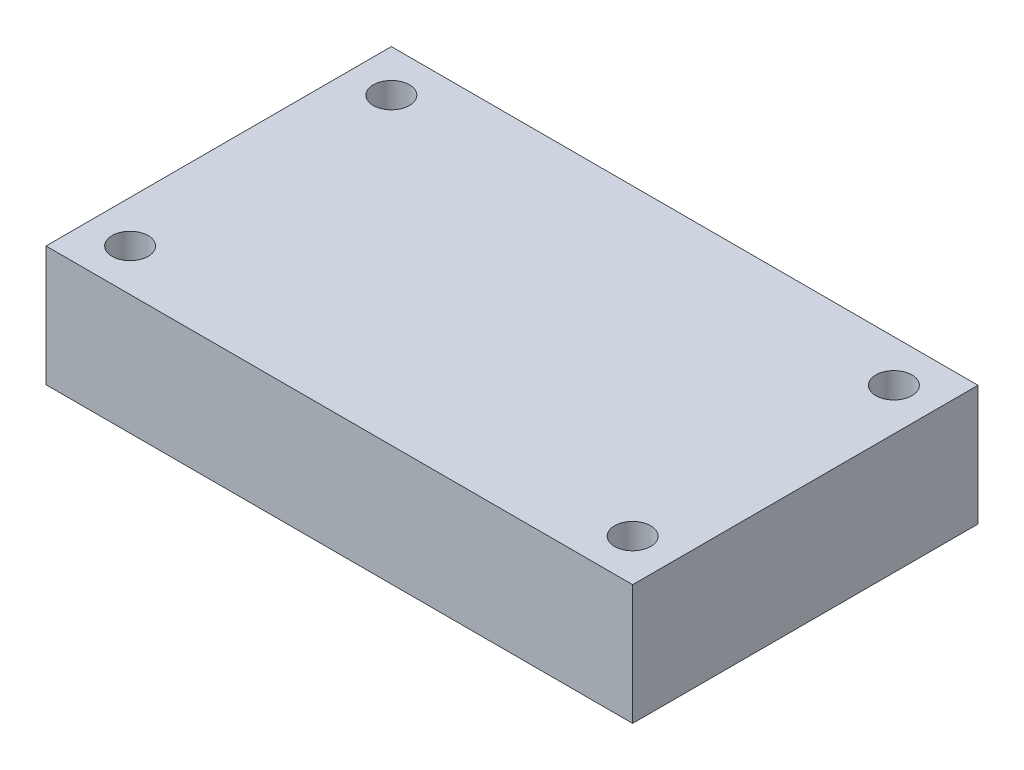
SolidWorks part; units mm, degrees
ref_plane "Front Plane" through (0, 0, 0) normal (0, 0, 1) x (1, 0, 0)
ref_plane "Top Plane" through (0, 0, 0) normal (0, 1, 0) x (1, 0, 0)
ref_plane "Right Plane" through (0, 0, 0) normal (1, 0, 0) x (0, 0, -1)
sketch "Sketch1" plane through (0, 0, 0) normal (0, 1, 0) x (1, 0, 0)
  line L1 (-31, -18.25) -> (31, -18.25)
  line L2 (-31, -18.25) -> (-31, 18.25)
  line L3 (-31, 18.25) -> (31, 18.25)
  line L4 (31, -18.25) -> (31, 18.25)
  line L5 (-31, -18.25) -> (31, 18.25) construction
  line L6 (-31, 18.25) -> (31, -18.25) construction
  point P0 (0, 0)
  dimension "D1" = 62
  dimension "D2" = 36.5
extrude "Boss-Extrude1" add sketch "Sketch1" along normal blind 12.7
sketch "Sketch2" plane through (0, 12.7, 0) normal (0, 1, 0) x (1, 0, 0)
  circle A0 centre (26.555, 13.805) radius 1.905
  circle A1 centre (26.555, -13.805) radius 1.905
  circle A2 centre (-26.555, 13.805) radius 1.905
  circle A3 centre (-26.555, -13.805) radius 1.905
extrude "Cut-Extrude1" cut sketch "Sketch2" against normal up to surface (12.7 mm away) up to face at (0, 0, 0)
